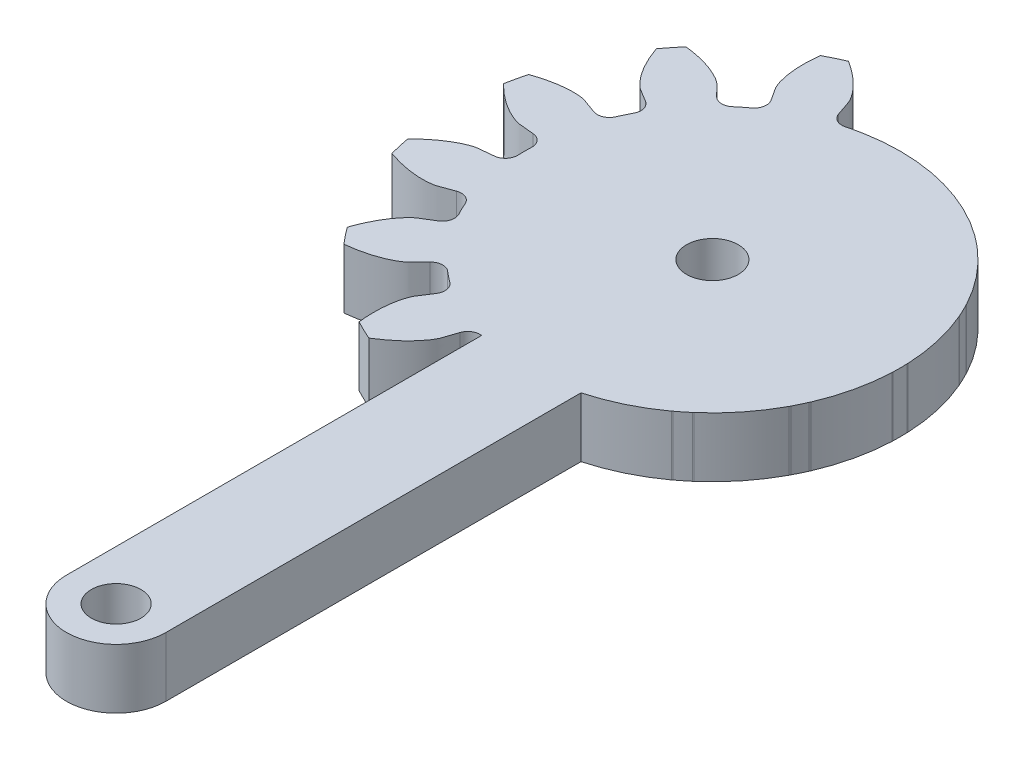
SolidWorks part; units mm, degrees
ref_plane "Front Plane" through (0, 0, 0) normal (0, 0, 1) x (1, 0, 0)
ref_plane "Top Plane" through (0, 0, 0) normal (0, 1, 0) x (1, 0, 0)
ref_plane "Right Plane" through (0, 0, 0) normal (1, 0, 0) x (0, 0, -1)
ref_plane "Plane1" through (0, 2.5, 0) normal (0, 1, 0) x (1, 0, 0)
sketch "Sketch1" plane through (0, 2.5, 0) normal (0, 1, 0) x (1, 0, 0)
  line L0 (-9, -29) -> (-9, -8.1136)
  line L1 (-14, -8.1136) -> (-14, -29)
  arc A0 (-9, -8.1136) -> (-8.3269, -8.5263) centre (-8.9077, -8.7184) cw
  arc A1 (-6.2794, -11.0615) -> (-5.3249, -10.6018) centre (-11.5, 1) ccw
  arc A2 (-6.0305, -7.4203) -> (-5.8819, -6.5942) centre (-5.5181, -7.086) cw
  arc A3 (-5.8819, -6.5942) -> (-5.3463, -6.1671) centre (-11.5, 1) ccw
  arc A4 (-5.3463, -6.1671) -> (-4.5079, -6.2061) centre (-4.9478, -6.6312) cw
  arc A5 (-1.5631, -7.6019) -> (-0.9026, -6.7736) centre (-11.5, 1) ccw
  arc A6 (-2.9187, -4.2133) -> (-3.1433, -3.4046) centre (-2.6021, -3.6898) cw
  arc A7 (-3.1433, -3.4046) -> (-2.846, -2.7873) centre (-11.5, 1) ccw
  arc A8 (-2.846, -2.7873) -> (-2.0737, -2.4587) centre (-2.2856, -3.0326) cw
  arc A9 (1.1851, -2.4386) -> (1.4208, -1.4057) centre (-11.5, 1) ccw
  arc A10 (-1.5065, 0.0263) -> (-2.0598, 0.6575) centre (-1.4484, 0.6353) cw
  arc A11 (-2.0598, 0.6575) -> (-2.0598, 1.3425) centre (-11.5, 1) ccw
  arc A12 (-2.0598, 1.3425) -> (-1.5065, 1.9737) centre (-1.4484, 1.3647) cw
  arc A13 (1.4208, 3.4057) -> (1.1851, 4.4386) centre (-11.5, 1) ccw
  arc A14 (-2.0737, 4.4587) -> (-2.846, 4.7873) centre (-2.2856, 5.0326) cw
  arc A15 (-2.846, 4.7873) -> (-3.1433, 5.4046) centre (-11.5, 1) ccw
  arc A16 (-3.1433, 5.4046) -> (-2.9187, 6.2133) centre (-2.6021, 5.6898) cw
  arc A17 (-0.9026, 8.7736) -> (-1.5631, 9.6019) centre (-11.5, 1) ccw
  arc A18 (-4.5079, 8.2061) -> (-5.3463, 8.1671) centre (-4.9478, 8.6312) cw
  arc A19 (-5.3463, 8.1671) -> (-5.8819, 8.5942) centre (-11.5, 1) ccw
  arc A20 (-5.8819, 8.5942) -> (-6.0305, 9.4203) centre (-5.5181, 9.086) cw
  arc A21 (-5.3249, 12.6018) -> (-6.2794, 13.0615) centre (-11.5, 1) ccw
  arc A22 (-8.3269, 10.5263) -> (-9.0654, 10.1273) centre (-8.9077, 10.7184) cw
  arc A23 (-9.0654, 10.1273) -> (-9.7333, 10.2798) centre (-11.5, 1) ccw
  arc A24 (-9.7333, 10.2798) -> (-10.2256, 10.9596) centre (-9.6189, 10.8807) cw
  arc A25 (-10.9703, 14.1322) -> (-12.0297, 14.1322) centre (-11.5, 1) ccw
  arc A26 (-12.7744, 10.9596) -> (-13.2667, 10.2798) centre (-13.3811, 10.8807) cw
  arc A27 (-13.2667, 10.2798) -> (-13.9346, 10.1273) centre (-11.5, 1) ccw
  arc A28 (-13.9346, 10.1273) -> (-14.6731, 10.5263) centre (-14.0923, 10.7184) cw
  arc A29 (-16.7206, 13.0615) -> (-17.6751, 12.6018) centre (-11.5, 1) ccw
  arc A30 (-16.9695, 9.4203) -> (-17.1181, 8.5942) centre (-17.4819, 9.086) cw
  arc A31 (-17.1181, 8.5942) -> (-17.6537, 8.1671) centre (-11.5, 1) ccw
  arc A32 (-17.6537, 8.1671) -> (-18.4921, 8.2061) centre (-18.0522, 8.6312) cw
  arc A33 (-21.4369, 9.6019) -> (-22.0974, 8.7736) centre (-11.5, 1) ccw
  arc A34 (-20.0813, 6.2133) -> (-19.8567, 5.4046) centre (-20.3979, 5.6898) cw
  arc A35 (-19.8567, 5.4046) -> (-20.154, 4.7873) centre (-11.5, 1) ccw
  arc A36 (-20.154, 4.7873) -> (-20.9263, 4.4587) centre (-20.7144, 5.0326) cw
  arc A37 (-24.1851, 4.4386) -> (-24.4208, 3.4057) centre (-11.5, 1) ccw
  arc A38 (-21.4935, 1.9737) -> (-20.9402, 1.3425) centre (-21.5516, 1.3647) cw
  arc A39 (-20.9402, 1.3425) -> (-20.9402, 0.6575) centre (-11.5, 1) ccw
  arc A40 (-20.9402, 0.6575) -> (-21.4935, 0.0263) centre (-21.5516, 0.6353) cw
  arc A41 (-24.4208, -1.4057) -> (-24.1851, -2.4386) centre (-11.5, 1) ccw
  arc A42 (-20.9263, -2.4587) -> (-20.154, -2.7873) centre (-20.7144, -3.0326) cw
  arc A43 (-20.154, -2.7873) -> (-19.8567, -3.4046) centre (-11.5, 1) ccw
  arc A44 (-19.8567, -3.4046) -> (-20.0813, -4.2133) centre (-20.3979, -3.6898) cw
  arc A45 (-22.0974, -6.7736) -> (-21.4369, -7.6019) centre (-11.5, 1) ccw
  arc A46 (-18.4921, -6.2061) -> (-17.6537, -6.1671) centre (-18.0522, -6.6312) cw
  arc A47 (-17.6537, -6.1671) -> (-17.1181, -6.5942) centre (-11.5, 1) ccw
  arc A48 (-17.1181, -6.5942) -> (-16.9695, -7.4203) centre (-17.4819, -7.086) cw
  arc A49 (-17.6751, -10.6018) -> (-16.7206, -11.0615) centre (-11.5, 1) ccw
  arc A50 (-14.6731, -8.5263) -> (-14, -8.1136) centre (-14.0923, -8.7184) cw
  arc A51 (-14, -29) -> (-9, -29) centre (-11.5, -29) ccw
  circle A52 centre (-11.5, 1) radius 1.3
  circle A53 centre (-11.5, -29) radius 1
  spline S0 degree 3 poles (-8.3269, -8.5263) (-8.2061, -8.8914) (-8.0828, -9.2613) (-8.0643, -9.2986) (-8.0323, -9.3674) (-7.9883, -9.4478) (-7.9247, -9.5526) (-7.8413, -9.6752) (-7.7354, -9.8155) (-7.6054, -9.9709) (-7.4494, -10.1395) (-7.2658, -10.319) (-7.0533, -10.507) (-6.8102, -10.7008) (-6.5522, -10.8879) (-6.3665, -11.0064) (-6.2794, -11.0615) knots 0.056244 0.056244 0.056244 0.056244 0.172234 0.201817 0.240008 0.285196 0.336434 0.39308 0.454661 0.520809 0.59123 0.665677 0.743945 0.825855 0.911253 0.985951 0.985951 0.985951 0.985951
  spline S1 degree 3 poles (-6.0305, -7.4203) (-5.8203, -7.7425) (-5.608, -8.0695) (-5.5903, -8.1072) (-5.5565, -8.1751) (-5.5211, -8.2597) (-5.4788, -8.3747) (-5.4349, -8.5164) (-5.3913, -8.6866) (-5.3508, -8.8852) (-5.3163, -9.1123) (-5.2905, -9.3677) (-5.276, -9.6511) (-5.2759, -9.962) (-5.2906, -10.2803) (-5.3137, -10.4994) (-5.3249, -10.6018) knots 0.056244 0.056244 0.056244 0.056244 0.172234 0.201817 0.240008 0.285196 0.336434 0.39308 0.454661 0.520809 0.59123 0.665677 0.743945 0.825855 0.911253 0.985951 0.985951 0.985951 0.985951
  spline S2 degree 3 poles (-4.5079, -6.2061) (-4.2406, -6.4827) (-3.969, -6.7624) (-3.9362, -6.788) (-3.8775, -6.8362) (-3.8029, -6.8894) (-3.7002, -6.9563) (-3.5718, -7.0306) (-3.4156, -7.111) (-3.231, -7.1946) (-3.0173, -7.2788) (-2.774, -7.3609) (-2.501, -7.4381) (-2.1978, -7.5073) (-1.8842, -7.5638) (-1.6655, -7.5901) (-1.5631, -7.6019) knots 0.056244 0.056244 0.056244 0.056244 0.172234 0.201817 0.240008 0.285196 0.336434 0.39308 0.454661 0.520809 0.59123 0.665677 0.743945 0.825855 0.911253 0.985951 0.985951 0.985951 0.985951
  spline S3 degree 3 poles (-2.9187, -4.2133) (-2.5895, -4.4124) (-2.2564, -4.6149) (-2.2241, -4.6412) (-2.1641, -4.6877) (-2.0956, -4.7485) (-2.0076, -4.8338) (-1.9066, -4.9424) (-1.7934, -5.0768) (-1.6708, -5.2382) (-1.5411, -5.4278) (-1.407, -5.6468) (-1.271, -5.8958) (-1.1361, -6.1759) (-1.0112, -6.4691) (-0.9369, -6.6764) (-0.9026, -6.7736) knots 0.056244 0.056244 0.056244 0.056244 0.172234 0.201817 0.240008 0.285196 0.336434 0.39308 0.454661 0.520809 0.59123 0.665677 0.743945 0.825855 0.911253 0.985951 0.985951 0.985951 0.985951
  spline S4 degree 3 poles (-2.0737, -2.4587) (-1.7128, -2.5919) (-1.3468, -2.7261) (-1.3061, -2.7349) (-1.2324, -2.7529) (-1.1421, -2.7685) (-1.0205, -2.7841) (-0.8726, -2.7954) (-0.6969, -2.8001) (-0.4943, -2.7953) (-0.2653, -2.7785) (-0.0105, -2.7468) (0.269, -2.6979) (0.5721, -2.6287) (0.8792, -2.5436) (1.0876, -2.4724) (1.1851, -2.4386) knots 0.056244 0.056244 0.056244 0.056244 0.172234 0.201817 0.240008 0.285196 0.336434 0.39308 0.454661 0.520809 0.59123 0.665677 0.743945 0.825855 0.911253 0.985951 0.985951 0.985951 0.985951
  spline S5 degree 3 poles (-1.5065, 0.0263) (-1.1236, -0.0103) (-0.7356, -0.0482) (-0.6951, -0.0579) (-0.6209, -0.0738) (-0.5327, -0.0988) (-0.4164, -0.1375) (-0.2783, -0.1915) (-0.118, -0.2635) (0.0625, -0.3557) (0.2616, -0.4703) (0.4774, -0.6094) (0.708, -0.7747) (0.9511, -0.9685) (1.1908, -1.1785) (1.3477, -1.3331) (1.4208, -1.4057) knots 0.056244 0.056244 0.056244 0.056244 0.172234 0.201817 0.240008 0.285196 0.336434 0.39308 0.454661 0.520809 0.59123 0.665677 0.743945 0.825855 0.911253 0.985951 0.985951 0.985951 0.985951
  spline S6 degree 3 poles (-1.5065, 1.9737) (-1.1236, 2.0103) (-0.7356, 2.0482) (-0.6951, 2.0579) (-0.6209, 2.0738) (-0.5327, 2.0988) (-0.4164, 2.1375) (-0.2783, 2.1915) (-0.118, 2.2635) (0.0625, 2.3557) (0.2616, 2.4703) (0.4774, 2.6094) (0.708, 2.7747) (0.9511, 2.9685) (1.1908, 3.1785) (1.3477, 3.3331) (1.4208, 3.4057) knots 0.056244 0.056244 0.056244 0.056244 0.172234 0.201817 0.240008 0.285196 0.336434 0.39308 0.454661 0.520809 0.59123 0.665677 0.743945 0.825855 0.911253 0.985951 0.985951 0.985951 0.985951
  spline S7 degree 3 poles (-2.0737, 4.4587) (-1.7128, 4.5919) (-1.3468, 4.7261) (-1.3061, 4.7349) (-1.2324, 4.7529) (-1.1421, 4.7685) (-1.0205, 4.7841) (-0.8726, 4.7954) (-0.6969, 4.8001) (-0.4943, 4.7953) (-0.2653, 4.7785) (-0.0105, 4.7468) (0.269, 4.6979) (0.5721, 4.6287) (0.8792, 4.5436) (1.0876, 4.4724) (1.1851, 4.4386) knots 0.056244 0.056244 0.056244 0.056244 0.172234 0.201817 0.240008 0.285196 0.336434 0.39308 0.454661 0.520809 0.59123 0.665677 0.743945 0.825855 0.911253 0.985951 0.985951 0.985951 0.985951
  spline S8 degree 3 poles (-2.9187, 6.2133) (-2.5895, 6.4124) (-2.2564, 6.6149) (-2.2241, 6.6412) (-2.1641, 6.6877) (-2.0956, 6.7485) (-2.0076, 6.8338) (-1.9066, 6.9424) (-1.7934, 7.0768) (-1.6708, 7.2382) (-1.5411, 7.4278) (-1.407, 7.6468) (-1.271, 7.8958) (-1.1361, 8.1759) (-1.0112, 8.4691) (-0.9369, 8.6764) (-0.9026, 8.7736) knots 0.056244 0.056244 0.056244 0.056244 0.172234 0.201817 0.240008 0.285196 0.336434 0.39308 0.454661 0.520809 0.59123 0.665677 0.743945 0.825855 0.911253 0.985951 0.985951 0.985951 0.985951
  spline S9 degree 3 poles (-4.5079, 8.2061) (-4.2406, 8.4827) (-3.969, 8.7624) (-3.9362, 8.788) (-3.8775, 8.8362) (-3.8029, 8.8894) (-3.7002, 8.9563) (-3.5718, 9.0306) (-3.4156, 9.111) (-3.231, 9.1946) (-3.0173, 9.2788) (-2.774, 9.3609) (-2.501, 9.4381) (-2.1978, 9.5073) (-1.8842, 9.5638) (-1.6655, 9.5901) (-1.5631, 9.6019) knots 0.056244 0.056244 0.056244 0.056244 0.172234 0.201817 0.240008 0.285196 0.336434 0.39308 0.454661 0.520809 0.59123 0.665677 0.743945 0.825855 0.911253 0.985951 0.985951 0.985951 0.985951
  spline S10 degree 3 poles (-6.0305, 9.4203) (-5.8203, 9.7425) (-5.608, 10.0695) (-5.5903, 10.1072) (-5.5565, 10.1751) (-5.5211, 10.2597) (-5.4788, 10.3747) (-5.4349, 10.5164) (-5.3913, 10.6866) (-5.3508, 10.8852) (-5.3163, 11.1123) (-5.2905, 11.3677) (-5.276, 11.6511) (-5.2759, 11.962) (-5.2906, 12.2803) (-5.3137, 12.4994) (-5.3249, 12.6018) knots 0.056244 0.056244 0.056244 0.056244 0.172234 0.201817 0.240008 0.285196 0.336434 0.39308 0.454661 0.520809 0.59123 0.665677 0.743945 0.825855 0.911253 0.985951 0.985951 0.985951 0.985951
  spline S11 degree 3 poles (-8.3269, 10.5263) (-8.2061, 10.8914) (-8.0828, 11.2613) (-8.0643, 11.2986) (-8.0323, 11.3674) (-7.9883, 11.4478) (-7.9247, 11.5526) (-7.8413, 11.6752) (-7.7354, 11.8155) (-7.6054, 11.9709) (-7.4494, 12.1395) (-7.2658, 12.319) (-7.0533, 12.507) (-6.8102, 12.7008) (-6.5522, 12.8879) (-6.3665, 13.0064) (-6.2794, 13.0615) knots 0.056244 0.056244 0.056244 0.056244 0.172234 0.201817 0.240008 0.285196 0.336434 0.39308 0.454661 0.520809 0.59123 0.665677 0.743945 0.825855 0.911253 0.985951 0.985951 0.985951 0.985951
  spline S12 degree 3 poles (-10.2256, 10.9596) (-10.176, 11.3411) (-10.1266, 11.7278) (-10.1271, 11.7694) (-10.126, 11.8453) (-10.1308, 11.9368) (-10.1426, 12.0588) (-10.1646, 12.2055) (-10.1991, 12.3778) (-10.2488, 12.5743) (-10.3162, 12.7939) (-10.4038, 13.0352) (-10.5137, 13.2968) (-10.6486, 13.5769) (-10.7999, 13.8574) (-10.9157, 14.0447) (-10.9703, 14.1322) knots 0.056244 0.056244 0.056244 0.056244 0.172234 0.201817 0.240008 0.285196 0.336434 0.39308 0.454661 0.520809 0.59123 0.665677 0.743945 0.825855 0.911253 0.985951 0.985951 0.985951 0.985951
  spline S13 degree 3 poles (-12.7744, 10.9596) (-12.824, 11.3411) (-12.8734, 11.7278) (-12.8729, 11.7694) (-12.874, 11.8453) (-12.8692, 11.9368) (-12.8574, 12.0588) (-12.8354, 12.2055) (-12.8009, 12.3778) (-12.7512, 12.5743) (-12.6838, 12.7939) (-12.5962, 13.0352) (-12.4863, 13.2968) (-12.3514, 13.5769) (-12.2001, 13.8574) (-12.0843, 14.0447) (-12.0297, 14.1322) knots 0.056244 0.056244 0.056244 0.056244 0.172234 0.201817 0.240008 0.285196 0.336434 0.39308 0.454661 0.520809 0.59123 0.665677 0.743945 0.825855 0.911253 0.985951 0.985951 0.985951 0.985951
  spline S14 degree 3 poles (-14.6731, 10.5263) (-14.7939, 10.8914) (-14.9172, 11.2613) (-14.9357, 11.2986) (-14.9677, 11.3674) (-15.0117, 11.4478) (-15.0753, 11.5526) (-15.1587, 11.6752) (-15.2646, 11.8155) (-15.3946, 11.9709) (-15.5506, 12.1395) (-15.7342, 12.319) (-15.9467, 12.507) (-16.1898, 12.7008) (-16.4478, 12.8879) (-16.6335, 13.0064) (-16.7206, 13.0615) knots 0.056244 0.056244 0.056244 0.056244 0.172234 0.201817 0.240008 0.285196 0.336434 0.39308 0.454661 0.520809 0.59123 0.665677 0.743945 0.825855 0.911253 0.985951 0.985951 0.985951 0.985951
  spline S15 degree 3 poles (-16.9695, 9.4203) (-17.1797, 9.7425) (-17.392, 10.0695) (-17.4097, 10.1072) (-17.4435, 10.1751) (-17.4789, 10.2597) (-17.5212, 10.3747) (-17.5651, 10.5164) (-17.6087, 10.6866) (-17.6492, 10.8852) (-17.6837, 11.1123) (-17.7095, 11.3677) (-17.724, 11.6511) (-17.7241, 11.962) (-17.7094, 12.2803) (-17.6863, 12.4994) (-17.6751, 12.6018) knots 0.056244 0.056244 0.056244 0.056244 0.172234 0.201817 0.240008 0.285196 0.336434 0.39308 0.454661 0.520809 0.59123 0.665677 0.743945 0.825855 0.911253 0.985951 0.985951 0.985951 0.985951
  spline S16 degree 3 poles (-18.4921, 8.2061) (-18.7594, 8.4827) (-19.031, 8.7624) (-19.0638, 8.788) (-19.1225, 8.8362) (-19.1971, 8.8894) (-19.2998, 8.9563) (-19.4282, 9.0306) (-19.5844, 9.111) (-19.769, 9.1946) (-19.9827, 9.2788) (-20.226, 9.3609) (-20.499, 9.4381) (-20.8022, 9.5073) (-21.1158, 9.5638) (-21.3345, 9.5901) (-21.4369, 9.6019) knots 0.056244 0.056244 0.056244 0.056244 0.172234 0.201817 0.240008 0.285196 0.336434 0.39308 0.454661 0.520809 0.59123 0.665677 0.743945 0.825855 0.911253 0.985951 0.985951 0.985951 0.985951
  spline S17 degree 3 poles (-20.0813, 6.2133) (-20.4105, 6.4124) (-20.7436, 6.6149) (-20.7759, 6.6412) (-20.8359, 6.6877) (-20.9044, 6.7485) (-20.9924, 6.8338) (-21.0934, 6.9424) (-21.2066, 7.0768) (-21.3292, 7.2382) (-21.4589, 7.4278) (-21.593, 7.6468) (-21.729, 7.8958) (-21.8639, 8.1759) (-21.9888, 8.4691) (-22.0631, 8.6764) (-22.0974, 8.7736) knots 0.056244 0.056244 0.056244 0.056244 0.172234 0.201817 0.240008 0.285196 0.336434 0.39308 0.454661 0.520809 0.59123 0.665677 0.743945 0.825855 0.911253 0.985951 0.985951 0.985951 0.985951
  spline S18 degree 3 poles (-20.9263, 4.4587) (-21.2872, 4.5919) (-21.6532, 4.7261) (-21.6939, 4.7349) (-21.7676, 4.7529) (-21.8579, 4.7685) (-21.9795, 4.7841) (-22.1274, 4.7954) (-22.3031, 4.8001) (-22.5057, 4.7953) (-22.7347, 4.7785) (-22.9895, 4.7468) (-23.269, 4.6979) (-23.5721, 4.6287) (-23.8792, 4.5436) (-24.0876, 4.4724) (-24.1851, 4.4386) knots 0.056244 0.056244 0.056244 0.056244 0.172234 0.201817 0.240008 0.285196 0.336434 0.39308 0.454661 0.520809 0.59123 0.665677 0.743945 0.825855 0.911253 0.985951 0.985951 0.985951 0.985951
  spline S19 degree 3 poles (-21.4935, 1.9737) (-21.8764, 2.0103) (-22.2644, 2.0482) (-22.3049, 2.0579) (-22.3791, 2.0738) (-22.4673, 2.0988) (-22.5836, 2.1375) (-22.7217, 2.1915) (-22.882, 2.2635) (-23.0625, 2.3557) (-23.2616, 2.4703) (-23.4774, 2.6094) (-23.708, 2.7747) (-23.9511, 2.9685) (-24.1908, 3.1785) (-24.3477, 3.3331) (-24.4208, 3.4057) knots 0.056244 0.056244 0.056244 0.056244 0.172234 0.201817 0.240008 0.285196 0.336434 0.39308 0.454661 0.520809 0.59123 0.665677 0.743945 0.825855 0.911253 0.985951 0.985951 0.985951 0.985951
  spline S20 degree 3 poles (-21.4935, 0.0263) (-21.8764, -0.0103) (-22.2644, -0.0482) (-22.3049, -0.0579) (-22.3791, -0.0738) (-22.4673, -0.0988) (-22.5836, -0.1375) (-22.7217, -0.1915) (-22.882, -0.2635) (-23.0625, -0.3557) (-23.2616, -0.4703) (-23.4774, -0.6094) (-23.708, -0.7747) (-23.9511, -0.9685) (-24.1908, -1.1785) (-24.3477, -1.3331) (-24.4208, -1.4057) knots 0.056244 0.056244 0.056244 0.056244 0.172234 0.201817 0.240008 0.285196 0.336434 0.39308 0.454661 0.520809 0.59123 0.665677 0.743945 0.825855 0.911253 0.985951 0.985951 0.985951 0.985951
  spline S21 degree 3 poles (-20.9263, -2.4587) (-21.2872, -2.5919) (-21.6532, -2.7261) (-21.6939, -2.7349) (-21.7676, -2.7529) (-21.8579, -2.7685) (-21.9795, -2.7841) (-22.1274, -2.7954) (-22.3031, -2.8001) (-22.5057, -2.7953) (-22.7347, -2.7785) (-22.9895, -2.7468) (-23.269, -2.6979) (-23.5721, -2.6287) (-23.8792, -2.5436) (-24.0876, -2.4724) (-24.1851, -2.4386) knots 0.056244 0.056244 0.056244 0.056244 0.172234 0.201817 0.240008 0.285196 0.336434 0.39308 0.454661 0.520809 0.59123 0.665677 0.743945 0.825855 0.911253 0.985951 0.985951 0.985951 0.985951
  spline S22 degree 3 poles (-20.0813, -4.2133) (-20.4105, -4.4124) (-20.7436, -4.6149) (-20.7759, -4.6412) (-20.8359, -4.6877) (-20.9044, -4.7485) (-20.9924, -4.8338) (-21.0934, -4.9424) (-21.2066, -5.0768) (-21.3292, -5.2382) (-21.4589, -5.4278) (-21.593, -5.6468) (-21.729, -5.8958) (-21.8639, -6.1759) (-21.9888, -6.4691) (-22.0631, -6.6764) (-22.0974, -6.7736) knots 0.056244 0.056244 0.056244 0.056244 0.172234 0.201817 0.240008 0.285196 0.336434 0.39308 0.454661 0.520809 0.59123 0.665677 0.743945 0.825855 0.911253 0.985951 0.985951 0.985951 0.985951
  spline S23 degree 3 poles (-18.4921, -6.2061) (-18.7594, -6.4827) (-19.031, -6.7624) (-19.0638, -6.788) (-19.1225, -6.8362) (-19.1971, -6.8894) (-19.2998, -6.9563) (-19.4282, -7.0306) (-19.5844, -7.111) (-19.769, -7.1946) (-19.9827, -7.2788) (-20.226, -7.3609) (-20.499, -7.4381) (-20.8022, -7.5073) (-21.1158, -7.5638) (-21.3345, -7.5901) (-21.4369, -7.6019) knots 0.056244 0.056244 0.056244 0.056244 0.172234 0.201817 0.240008 0.285196 0.336434 0.39308 0.454661 0.520809 0.59123 0.665677 0.743945 0.825855 0.911253 0.985951 0.985951 0.985951 0.985951
  spline S24 degree 3 poles (-16.9695, -7.4203) (-17.1797, -7.7425) (-17.392, -8.0695) (-17.4097, -8.1072) (-17.4435, -8.1751) (-17.4789, -8.2597) (-17.5212, -8.3747) (-17.5651, -8.5164) (-17.6087, -8.6866) (-17.6492, -8.8852) (-17.6837, -9.1123) (-17.7095, -9.3677) (-17.724, -9.6511) (-17.7241, -9.962) (-17.7094, -10.2803) (-17.6863, -10.4994) (-17.6751, -10.6018) knots 0.056244 0.056244 0.056244 0.056244 0.172234 0.201817 0.240008 0.285196 0.336434 0.39308 0.454661 0.520809 0.59123 0.665677 0.743945 0.825855 0.911253 0.985951 0.985951 0.985951 0.985951
  spline S25 degree 3 poles (-14.6731, -8.5263) (-14.7939, -8.8914) (-14.9172, -9.2613) (-14.9357, -9.2986) (-14.9677, -9.3674) (-15.0117, -9.4478) (-15.0753, -9.5526) (-15.1587, -9.6752) (-15.2646, -9.8155) (-15.3946, -9.9709) (-15.5506, -10.1395) (-15.7342, -10.319) (-15.9467, -10.507) (-16.1898, -10.7008) (-16.4478, -10.8879) (-16.6335, -11.0064) (-16.7206, -11.0615) knots 0.056244 0.056244 0.056244 0.056244 0.172234 0.201817 0.240008 0.285196 0.336434 0.39308 0.454661 0.520809 0.59123 0.665677 0.743945 0.825855 0.911253 0.985951 0.985951 0.985951 0.985951
extrude "Boss-Extrude1" add sketch "Sketch1" against normal blind 3
sketch "Sketch4" plane through (0, -0.5, 0) normal (0, -1, 0) x (1, 0, 0)
  line L0 (-9, 8.1136) -> (-9, 12.5675)
  line L1 (-9, 29) -> (-9, 8.1136) construction
  line L2 (-9, 12.5675) -> (2.5069, 7.7618)
  line L3 (2.5069, 7.7618) -> (2.5069, -7.0602)
  line L4 (2.5069, -7.0602) -> (-4.7776, -15.2046)
  line L5 (-4.7776, -15.2046) -> (-13.8418, -15.2046)
  line L6 (-13.8418, -15.2046) -> (-13.9346, -10.1273)
  arc A0 (-9, 8.1136) -> (-13.9345, -10.1313) centre (-11.5, -1) cw
extrude "Cut-Extrude3" cut sketch "Sketch4" against normal blind 10 contours L0 A0 L6 L5 L4 L3 L2
sketch "Sketch5" plane through (0, -0.5, 0) normal (0, -1, 0) x (1, 0, 0)
  circle A0 centre (-11.5, 29) radius 1.25
  dimension "D1" = 2.5
extrude "Cut-Extrude4" cut sketch "Sketch5" against normal through all
